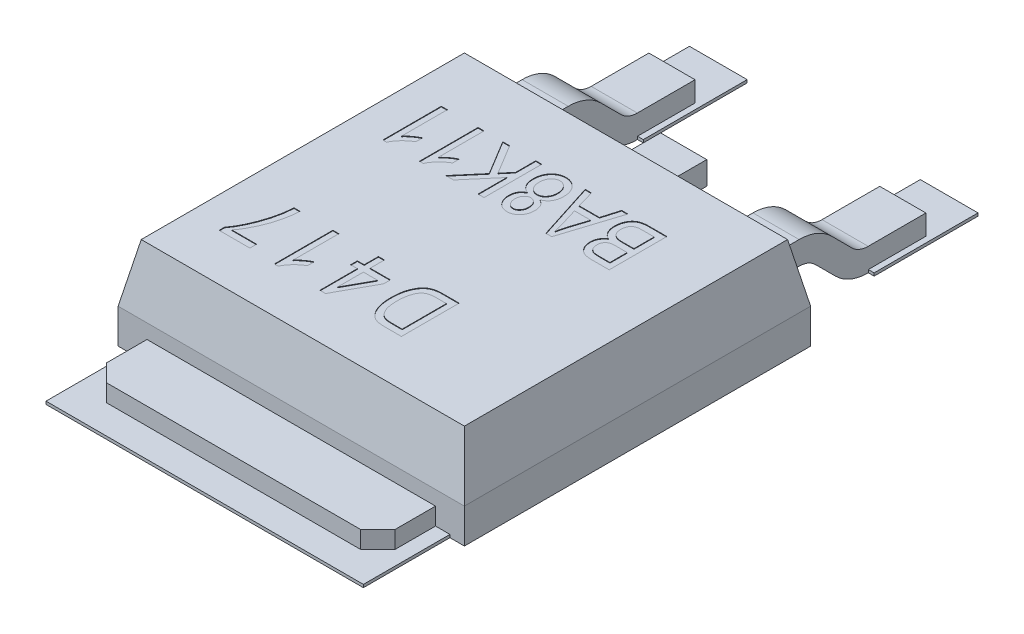
SolidWorks part; units mm, degrees
material "Pure Silver"
ref_plane "Front Plane" through (0, 0, 0) normal (0, 0, 1) x (1, 0, 0)
ref_plane "Top Plane" through (0, 0, 0) normal (0, 1, 0) x (1, 0, 0)
ref_plane "Right Plane" through (0, 0, 0) normal (1, 0, 0) x (0, 0, -1)
sketch "Sketch1" plane through (0, 0, 0) normal (0, 1, 0) x (1, 0, 0)
  line L0 (0, -0.88) -> (0, 0.88) construction
  line L1 (-3, 3) -> (3, 3)
  line L2 (-3, 3) -> (-3, -3)
  line L3 (-3, -3) -> (3, -3)
  line L4 (3, 3) -> (3, -3)
  line L5 (-0.88, 0) -> (0.88, 0) construction
  dimension "D1" = 6
  dimension "D2" = 3
  dimension "D3" = 6
  dimension "D4" = 3
extrude "Boss-Extrude1" add sketch "Sketch1" along normal blind 1.6
chamfer "Chamfer1" distance 1 distance2 0.2 4 edges at (-3, 1.6, 0) (0, 1.6, -3) (3, 1.6, 0) (0, 1.6, 3)
sketch "Esquisse1" plane through (0, 0, 0) normal (0, -1, 0) x (1, 0, 0)
  line L0 (-3, 3) -> (3, 3) construction
  line L1 (-2.5, 3) -> (-2.5, 3.7)
  line L2 (-2.5, 3.7) -> (-2.2, 4)
  line L3 (-2.2, 4) -> (2.2, 4)
  line L4 (2.2, 4) -> (2.5, 3.7)
  line L5 (2.5, 3.7) -> (2.5, 3)
  line L6 (2.5, 3) -> (-2.5, 3)
  dimension "D1" = 1
  dimension "D2" = 0.3
  dimension "D3" = 45
  dimension "D4" = 5
  dimension "D5" = 2.5
extrude "Boss.-Extru.1" add sketch "Esquisse1" against normal blind 0.35
ref_plane "Plane1" through (2, 0, 0) normal (1, 0, 0) x (0, 0, -1)
sketch "Sketch4" plane through (0, 0, 0) normal (0, 1, 0) x (1, 0, 0)
  line L0 (-2.75, -3.5) -> (2.75, -3.5) construction
  line L1 (-2.75, -2.5) -> (2.75, -2.5)
  line L2 (-2.75, -2.5) -> (-2.75, -4.5)
  line L3 (-2.75, -4.5) -> (2.75, -4.5)
  line L4 (2.75, -2.5) -> (2.75, -4.5)
  line L5 (-0.88, 0) -> (0.88, 0) construction
  line L6 (0, -0.88) -> (0, 0.88) construction
  line L7 (-2.5, 5.5) -> (-1.5, 5.5) construction
  line L8 (-2.5, 6.4) -> (-1.5, 6.4)
  line L9 (-2.5, 6.4) -> (-2.5, 4.6)
  line L10 (-2.5, 4.6) -> (-1.5, 4.6)
  line L11 (-1.5, 6.4) -> (-1.5, 4.6)
  line L12 (0, 0) -> (0, 7.9111) construction
  line L16 (1.5, 6.4) -> (2.5, 6.4)
  line L17 (1.5, 6.4) -> (1.5, 4.6)
  line L18 (1.5, 4.6) -> (2.5, 4.6)
  line L19 (2.5, 6.4) -> (2.5, 4.6)
  dimension "D1" = 3.5
  dimension "D2" = 1
  dimension "D3" = 5.5
  dimension "D4" = 2.75
  dimension "D5" = 1
  dimension "D6" = 3
  dimension "D8" = 5.5
  dimension "D10" = 1.8
extrude "Boss-Extrude2" add sketch "Sketch4" along normal blind 0.05
sketch "Sketch5" plane through (0, 1.6, 0) normal (0, 1, 0) x (1, 0, 0)
  line L0 (1, -1) -> (-2.199, -1) construction
  line L1 (0, -0.88) -> (0, 0.88) construction
  line L2 (-0.88, 0) -> (0.88, 0) construction
  text T0 "D417" font "Arial Narrow" height 1
  dimension "D1" = 1
  dimension "D2" = 1
sketch "Sketch6" plane through (0, 1.6, 0) normal (0, 1, 0) x (1, 0, 0)
  line L0 (1.8, 1.8) -> (-2.6137, 1.8) construction
  line L1 (-0.88, 0) -> (0.88, 0) construction
  line L2 (0, -0.88) -> (0, 0.88) construction
  text T0 "BA8K11" font "Arial Narrow" height 1
  dimension "D1" = 1.8
  dimension "D2" = 1.8
extrude "Cut-Extrude1" cut sketch "Sketch5" against normal blind 0.01
extrude "Cut-Extrude2" cut sketch "Sketch6" against normal blind 0.01
sketch "Esquisse2" plane through (2, 0, 0) normal (1, 0, 0) x (0, 0, -1)
  line L0 (2.8, 0.9) -> (3.4, 0.9)
  line L1 (3.8243, 0.7243) -> (4.1728, 0.3757)
  line L2 (4.5971, 0.2) -> (5.5971, 0.2)
  line L3 (-2.8, 1.6) -> (2.8, 1.6) construction
  line L4 (-3, 0) -> (3, 0) construction
  arc A0 (3.4, 0.9) -> (3.8243, 0.7243) centre (3.4, 0.3) cw
  arc A1 (4.1728, 0.3757) -> (4.5971, 0.2) centre (4.5971, 0.8) ccw
  dimension "D1" = 0.6
  dimension "D2" = 0.7
  dimension "D3" = 0.2
  dimension "D4" = 2.8
  dimension "D5" = 0.6
  dimension "D6" = 45
  dimension "D7" = 1
extrude "Extru.-Mince1" add sketch "Esquisse2" along direction (1, 0, 0) on the side of the normal mid plane 0.8 thin thin type mid plane wall 0.4
mirror "Symétrie1" about plane through (0, 0, 0) normal (1, 0, 0) of "Extru.-Mince1"
sketch "Esquisse3" plane through (0, 0, 0) normal (1, 0, 0) x (0, 0, -1)
  line L1 (2.8, 0.9) -> (3.8, 0.9)
  dimension "D1" = 1
extrude "Extru.-Mince2" add sketch "Esquisse3" along normal mid plane 0.8 thin thin type mid plane wall 0.4
